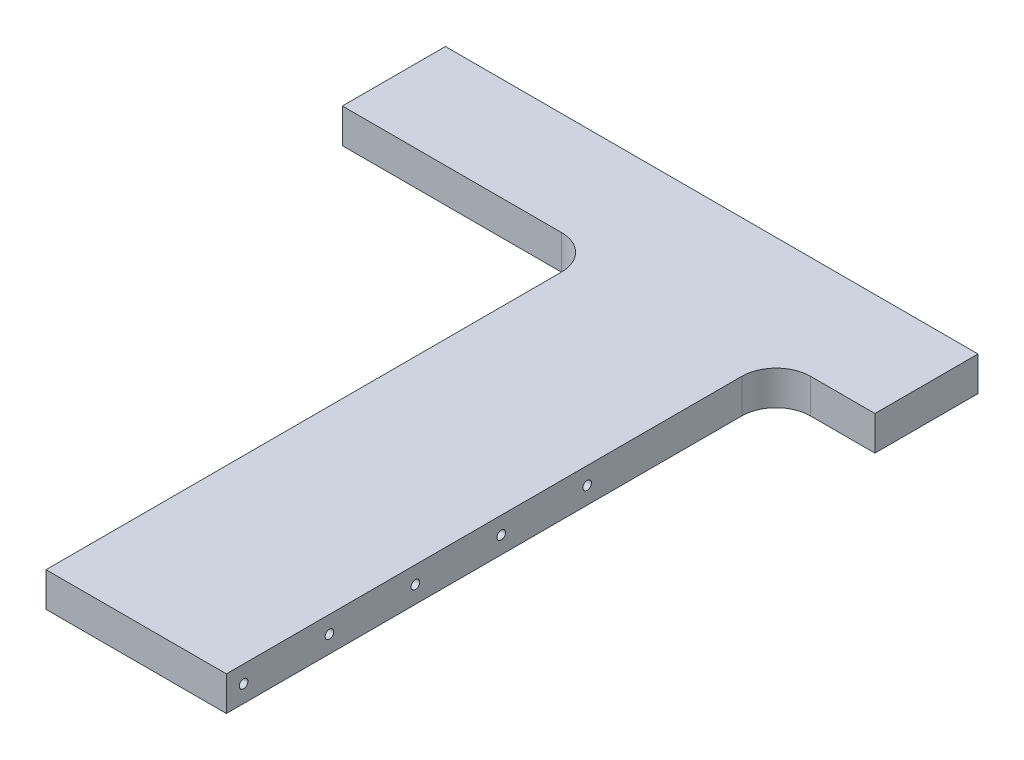
SolidWorks part; units mm, degrees
material "G.AL C330 (AlZn5,5Mg1,5)"
ref_plane "Ebene vorne" through (0, 0, 0) normal (0, 0, 1) x (1, 0, 0)
ref_plane "Ebene oben" through (0, 0, 0) normal (0, 1, 0) x (1, 0, 0)
ref_plane "Ebene rechts" through (0, 0, 0) normal (1, 0, 0) x (0, 0, -1)
sketch "Skizze1" plane through (0, 0, 0) normal (0, 1, 0) x (1, 0, 0)
  line L0 (0, 380) -> (0, 0) construction
  line L1 (-52.5, 0) -> (52.5, 0)
  line L2 (-52.5, 0) -> (-52.5, 320)
  line L3 (-200, 380) -> (110, 380)
  line L4 (52.5, 0) -> (52.5, 320)
  line L5 (110, 380) -> (110, 320)
  line L6 (-200, 380) -> (-200, 320)
  line L8 (110, 320) -> (52.5, 320)
  line L9 (-200, 320) -> (-52.5, 320)
  point P0 (0, 0)
  dimension "D1" = 105
  dimension "D2" = 200
  dimension "D3" = 380
  dimension "D4" = 60
  dimension "D5" = 110
extrude "Aufsatz-Linear austragen1" add sketch "Skizze1" along normal blind 20
hole_wizard "M6 Gewindebohrung1" positions "Skizze3" profile "Skizze4" tap size "M6" standard "DIN"
sketch "Skizze3" plane through (52.5, 0, 0) normal (1, 0, 0) x (0, 0, -1)
  point P33 (10, 10)
  point P36 (60, 10)
  point P39 (110, 10)
  point P42 (160, 10)
  point P45 (210, 60)
  point P62 (210, 10)
sketch "Skizze4" plane through (52.5, 10, -10) normal (0, 1, 0) x (0, 0, -1)
  line L0 (0, 0) -> (0, 18.5022)
  line L1 (0, 18.5022) -> (2.5, 17)
  line L2 (2.5, 17) -> (2.5, 0)
  line L5 (2.5, 0) -> (0, 0)
  line L10 (0, 18.5022) -> (-2.5, 17) construction
  line L11 (0, -6.35) -> (0, 107.95) construction
  dimension "Bohrerdurchmesser" = 5
  dimension "Bohrungstiefe" = 17
  dimension "Spitzenwinkel" = 118
cosmetic thread "Bohrungsgewinde1" parameters "D1"=12, "D2"=6
cosmetic thread "Bohrungsgewinde2" parameters "D1"=12, "D2"=6
cosmetic thread "Bohrungsgewinde3" parameters "D1"=12, "D2"=6
cosmetic thread "Bohrungsgewinde4" parameters "D1"=12, "D2"=6
cosmetic thread "Bohrungsgewinde5" parameters "D1"=12, "D2"=6
mirror "Spiegeln1" about plane through (0, 0, 0) normal (1, 0, 0) of "M6 Gewindebohrung1"
hole_wizard "M6 Gewindebohrung2" positions "Skizze5" profile "Skizze7" tap size "M6" standard "DIN"
sketch "Skizze5" plane through (0, 0, -380) normal (0, 0, -1) x (-1, 0, 0)
  line L0 (-110, 10) -> (200, 10) construction
  line L1 (-110, 20) -> (-110, 0) construction
  line L2 (200, 20) -> (200, 0) construction
  line L3 (0, 0) -> (0, 20) construction
  line L4 (-110, 20) -> (200, 20) construction
  point P0 (-90, 10)
  point P2 (180, 10)
  point P4 (0, 10)
  dimension "D1" = 20
  dimension "D2" = 20
sketch "Skizze7" plane through (90, 10, -380) normal (1, 0, 0) x (0, 1, 0)
  line L0 (0, 0) -> (0, 18.5022)
  line L1 (0, 18.5022) -> (2.5, 17)
  line L2 (2.5, 17) -> (2.5, 0)
  line L5 (2.5, 0) -> (0, 0)
  line L10 (0, 18.5022) -> (-2.5, 17) construction
  line L11 (0, -6.35) -> (0, 107.95) construction
  dimension "Bohrerdurchmesser" = 5
  dimension "Bohrungstiefe" = 17
  dimension "Spitzenwinkel" = 118
cosmetic thread "Bohrungsgewinde6" parameters "D1"=12, "D2"=6
cosmetic thread "Bohrungsgewinde7" parameters "D1"=12, "D2"=6
cosmetic thread "Bohrungsgewinde8" parameters "D1"=12, "D2"=6
fillet "Verrundung1" radius 20 2 edges at (52.5, 10, -320) (-52.5, 10, -320)
hole_wizard "Ø6.0mm Transitional Stiftloch1" positions "Skizze8" profile "Skizze9" hole size "Ø6.0" standard "DIN"
sketch "Skizze8" plane through (0, 0, -380) normal (0, 0, -1) x (-1, 0, 0)
  line L0 (-110, 10) -> (200, 10) construction
  line L1 (-110, 20) -> (-110, 0) construction
  line L2 (200, 20) -> (200, 0) construction
  point P13 (-30, 10)
  point P15 (120, 10)
  dimension "D1" = 80
  dimension "D2" = 150
sketch "Skizze9" plane through (-120, 10, -380) normal (1, 0, 0) x (0, 1, 0)
  line L0 (0, 0) -> (0, 18.8026)
  line L1 (0, 18.8026) -> (3, 17)
  line L2 (3, 17) -> (3, 0)
  line L5 (3, 0) -> (0, 0)
  line L10 (0, 18.8026) -> (-3, 17) construction
  line L11 (0, -6.35) -> (0, 107.95) construction
  dimension "Bohrerdurchmesser" = 6
  dimension "Bohrungstiefe" = 17
  dimension "Spitzenwinkel" = 118
